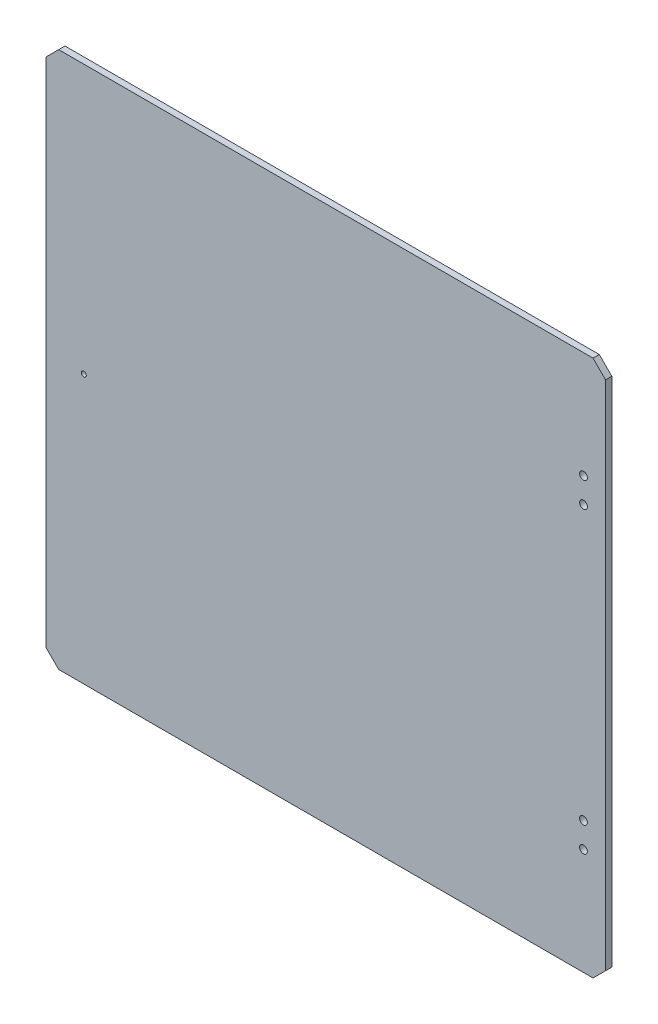
SolidWorks part; units mm, degrees
material "ABS PC"
ref_plane "Piano frontale" through (0, 0, 0) normal (0, 0, 1) x (1, 0, 0)
ref_plane "Piano superiore" through (0, 0, 0) normal (0, 1, 0) x (1, 0, 0)
ref_plane "Piano destro" through (0, 0, 0) normal (1, 0, 0) x (0, 0, -1)
sketch "Schizzo1" plane through (0, 0, 0) normal (0, 0, 1) x (1, 0, 0)
  line L0 (-223, 204) -> (-213, 214)
  line L1 (213, -214) -> (-213, -214)
  line L2 (223, 204) -> (223, -204)
  line L3 (213, 214) -> (-213, 214)
  line L4 (-223, -204) -> (-223, 204)
  line L5 (223, -214) -> (-223, 214) construction
  line L6 (223, 214) -> (-223, -214) construction
  line L7 (223, 204) -> (213, 214)
  line L8 (213, -214) -> (223, -204)
  line L9 (-213, -214) -> (-223, -204)
  line L11 (-223, 0) -> (221, 0) construction
  circle A0 centre (205.4, 129) radius 3.1
  circle A1 centre (205.4, 109) radius 3.1
  circle A2 centre (205.4, -109) radius 3.1
  circle A3 centre (205.4, -129) radius 3.1
  circle A4 centre (-193, 0) radius 2
  point P0 (0, 0)
  point P25 (223, -214)
  dimension "D9" = 4
  dimension "D12" = 6.2
  dimension "D1" = 446
  dimension "D2" = 428
  dimension "D3" = 20
  dimension "D4" = 17.6
  dimension "D10" = 30
  dimension "D11" = 85
extrude "Estrusione-Estrusione1" add sketch "Schizzo1" along normal blind 5
